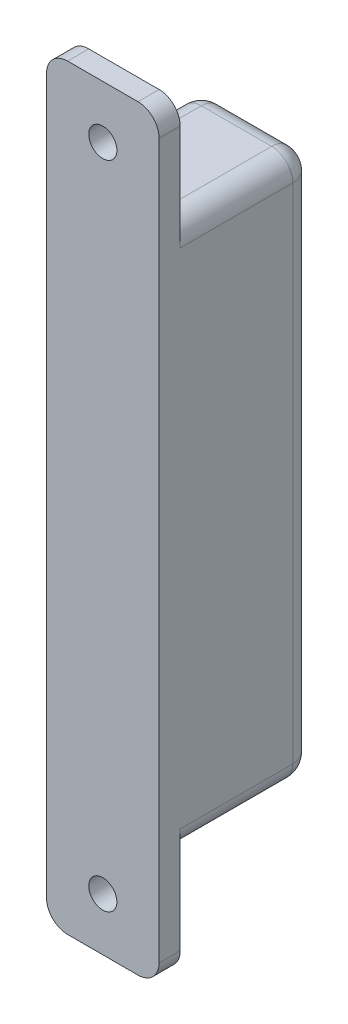
SolidWorks part; units mm, degrees
ref_plane "Front Plane" through (0, 0, 0) normal (0, 0, 1) x (1, 0, 0)
ref_plane "Top Plane" through (0, 0, 0) normal (0, 1, 0) x (1, 0, 0)
ref_plane "Right Plane" through (0, 0, 0) normal (1, 0, 0) x (0, 0, -1)
sketch "Sketch2" plane through (0, 0, 0) normal (0, 0, 1) x (1, 0, 0)
  line L0 (0, 0) -> (0, 77.5)
  line L1 (0, 77.5) -> (16, 77.5)
  line L2 (16, 77.5) -> (16, 0)
  line L3 (16, 0) -> (0, 0)
extrude "Boss-Extrude1" add sketch "Sketch2" against normal blind 19
sketch "Sketch3" plane through (0, 0, 0) normal (0, 0, 1) x (1, 0, 0)
  line L0 (0, 77.5) -> (0, 92.5)
  line L1 (0, 92.5) -> (16, 92.5)
  line L2 (16, 92.5) -> (16, 0)
  line L3 (16, 0) -> (16, -15)
  line L4 (16, -15) -> (0, -15)
  line L5 (0, -15) -> (0, 77.5)
extrude "Boss-Extrude2" add sketch "Sketch3" along normal blind 3
sketch "Sketch4" plane through (0, 0, 3) normal (0, 0, 1) x (1, 0, 0)
  line L1 (16, 77.5) -> (0, 77.5) construction
  line L2 (16, 77.5) -> (0, 77.5)
  line L3 (0, 77.5) -> (16, 92.5)
  line L4 (16, 38.75) -> (0, 38.75)
  line L5 (16, -15) -> (16, 92.5) construction
  line L6 (0, 92.5) -> (0, -15) construction
  circle A0 centre (8, 85) radius 2
  circle A1 centre (8, -7.5) radius 2
extrude "Cut-Extrude1" cut sketch "Sketch4" against normal through all contours A0 | A1
fillet "Fillet1" radius 3 8 edges at (0, 0, -9.5) (16, 0, -9.5) (16, 77.5, -9.5) (0, 77.5, -9.5) (8, 0, -19) (8, 77.5, -19) (16, 38.75, -19) (0, 38.75, -19)
fillet "Fillet2" radius 3 4 edges at (0, -15, 1.5) (16, -15, 1.5) (0, 92.5, 1.5) (16, 92.5, 1.5)
